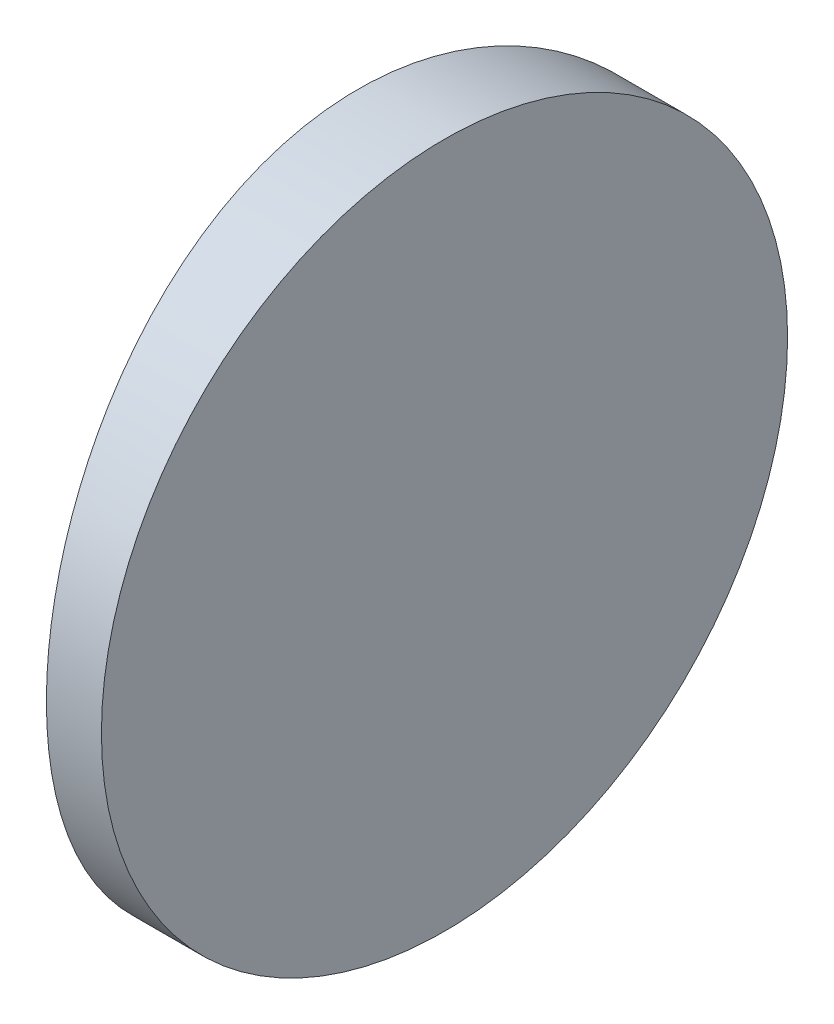
SolidWorks part; units mm, degrees
ref_plane "前视基准面" through (0, 0, 0) normal (0, 0, 1) x (1, 0, 0)
ref_plane "上视基准面" through (0, 0, 0) normal (0, 1, 0) x (1, 0, 0)
ref_plane "右视基准面" through (0, 0, 0) normal (1, 0, 0) x (0, 0, -1)
sketch "草图1" plane through (0, 0, 0) normal (0, 1, 0) x (1, 0, 0)
  line L0 (10.7432, 0) -> (-74.3321, 0) construction
  line L1 (-63.2794, 12.5) -> (-61.2748, 12.5)
  line L2 (-63.2794, -12.5) -> (-61.2748, -12.5)
  line L3 (-61.2748, 12.5) -> (-61.2748, -12.5)
  arc A0 (-63.2794, 12.5) -> (-63.2794, -12.5) centre (4.3552, 0) ccw
  point P2 (-74.3321, 0)
  point P19 (-64.4248, 0)
  point P20 (-61.2748, 0)
  dimension "D2" = 12.5
  dimension "D3" = 68.78
  dimension "D4" = 3.15
  dimension "D1" = 12.5
extrude "凸台-拉伸1" add sketch "草图1" along normal blind 25 contours A0 L2 L3 L1
sketch "草图2" plane through (-61.2748, 0, 0) normal (1, 0, 0) x (0, 0, -1)
  line L0 (12.5, 0) -> (-12.5, 0) construction
  line L7 (-12.5, 0) -> (12.5, 0)
  line L8 (12.5, 0) -> (12.5, 25)
  line L9 (12.5, 25) -> (-12.5, 25)
  line L10 (-12.5, 25) -> (-12.5, 0)
  line L11 (-12.5, 0) -> (12.5, 0)
  line L12 (12.5, 0) -> (12.5, 25)
  line L13 (12.5, 25) -> (-12.5, 25)
  line L14 (-12.5, 25) -> (-12.5, 0)
  circle A0 centre (0, 12.5) radius 12.5
  line M1 (-12.5, 0) -> (12.5, 0)
  line M2 (12.5, 0) -> (12.5, 25)
  line M3 (12.5, 25) -> (-12.5, 25)
  line M4 (-12.5, 25) -> (-12.5, 0)
  dimension "D1" = 25
  dimension "D4" = 12.5
  dimension "D2" = 12.5
  dimension "D3" = 0
extrude "切除-拉伸8" cut sketch "草图2" against normal blind 12.7 contours A0 L13 M4 | A0 L12 M3 | A0 L11 M2 | A0 L14 M1
